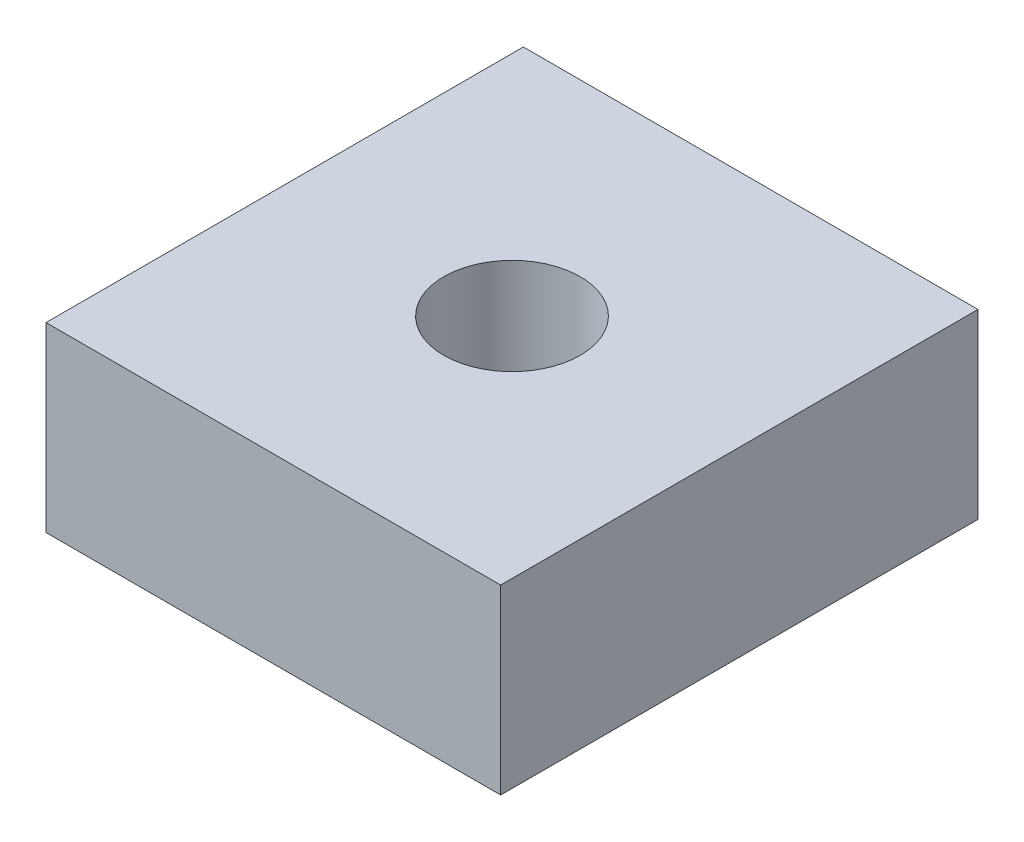
SolidWorks part; units mm, degrees
ref_plane "Front Plane" through (0, 0, 0) normal (0, 0, 1) x (1, 0, 0)
ref_plane "Top Plane" through (0, 0, 0) normal (0, 1, 0) x (1, 0, 0)
ref_plane "Right Plane" through (0, 0, 0) normal (1, 0, 0) x (0, 0, -1)
sketch "Sketch1" plane through (0, 0, 0) normal (0, 1, 0) x (1, 0, 0)
  line L1 (0, 0) -> (10, 0)
  line L2 (0, 0) -> (0, 10.5)
  line L3 (0, 10.5) -> (10, 10.5)
  line L4 (10, 0) -> (10, 10.5)
  dimension "D1" = 10.5
  dimension "D2" = 10
extrude "Boss-Extrude1" add sketch "Sketch1" along normal blind 4
sketch "Sketch2" plane through (0, 4, 0) normal (0, 1, 0) x (1, 0, 0)
  line L0 (0, 10.5) -> (10, 0) construction
  circle A0 centre (5, 5.25) radius 1.5
  point P6 (0, 0)
  point P7 (5, 5.25)
  dimension "D1" = 3
extrude "Cut-Extrude1" cut sketch "Sketch2" against normal blind 4
